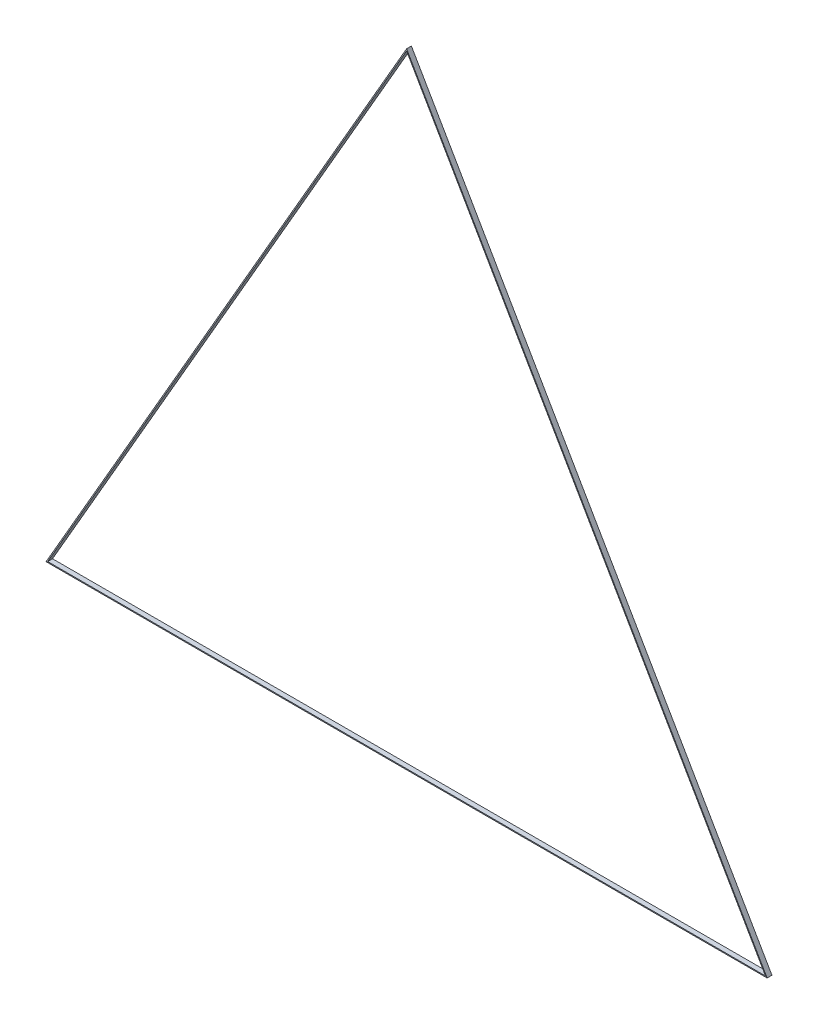
SolidWorks part; units mm, degrees
ref_plane "Plan de face" through (0, 0, 0) normal (0, 0, 1) x (1, 0, 0)
ref_plane "Plan de dessus" through (0, 0, 0) normal (0, 1, 0) x (1, 0, 0)
ref_plane "Plan de droite" through (0, 0, 0) normal (1, 0, 0) x (0, 0, -1)
sketch "Esquisse1" plane through (0, 0, 0) normal (0, 0, 1) x (1, 0, 0)
  line L0 (-750, 0) -> (0, 1299.0381)
  line L1 (0, 1299.0381) -> (750, 0)
  line L2 (750, 0) -> (-750, 0)
  point P2 (0, 0)
  dimension "D1" = 60
  dimension "D2" = 60
  dimension "D3" = 1500
extrude "Boss.-Extru.1" add sketch "Esquisse1" along normal blind 10
sketch "Esquisse2" plane through (0, 0, 10) normal (0, 0, 1) x (1, 0, 0)
  line L0 (-746.5359, 2) -> (0, 1295.0381)
  line L1 (0, 1295.0381) -> (746.5359, 2)
  line L2 (746.5359, 2) -> (-746.5359, 2)
  line L3 (-750, 0) -> (750, 0) construction
  line L4 (0, 1299.0381) -> (-750, 0) construction
  line L5 (750, 0) -> (0, 1299.0381) construction
  dimension "D1" = 2
  dimension "D2" = 2
  dimension "D3" = 2
extrude "Enlèv. mat.-Extru.1" cut sketch "Esquisse2" against normal blind 10
